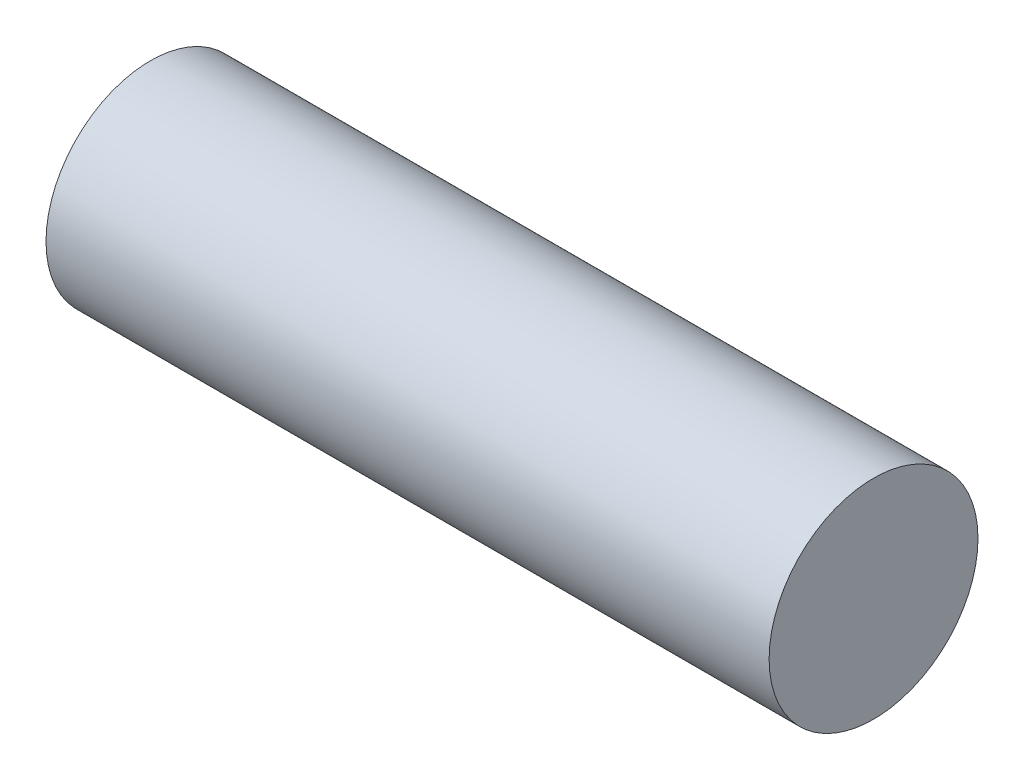
SolidWorks part; units mm, degrees
ref_plane "Przednia" through (0, 0, 0) normal (0, 0, 1) x (1, 0, 0)
ref_plane "Górna" through (0, 0, 0) normal (0, 1, 0) x (1, 0, 0)
ref_plane "Prawa" through (0, 0, 0) normal (1, 0, 0) x (0, 0, -1)
sketch "Szkic1" plane through (0, 0, 0) normal (1, 0, 0) x (0, 0, -1)
  circle A0 centre (0, 0) radius 2.6
  dimension "D1" = 5.2
extrude "Dodanie-wyciągnięcie1" add sketch "Szkic1" along normal mid plane 18
